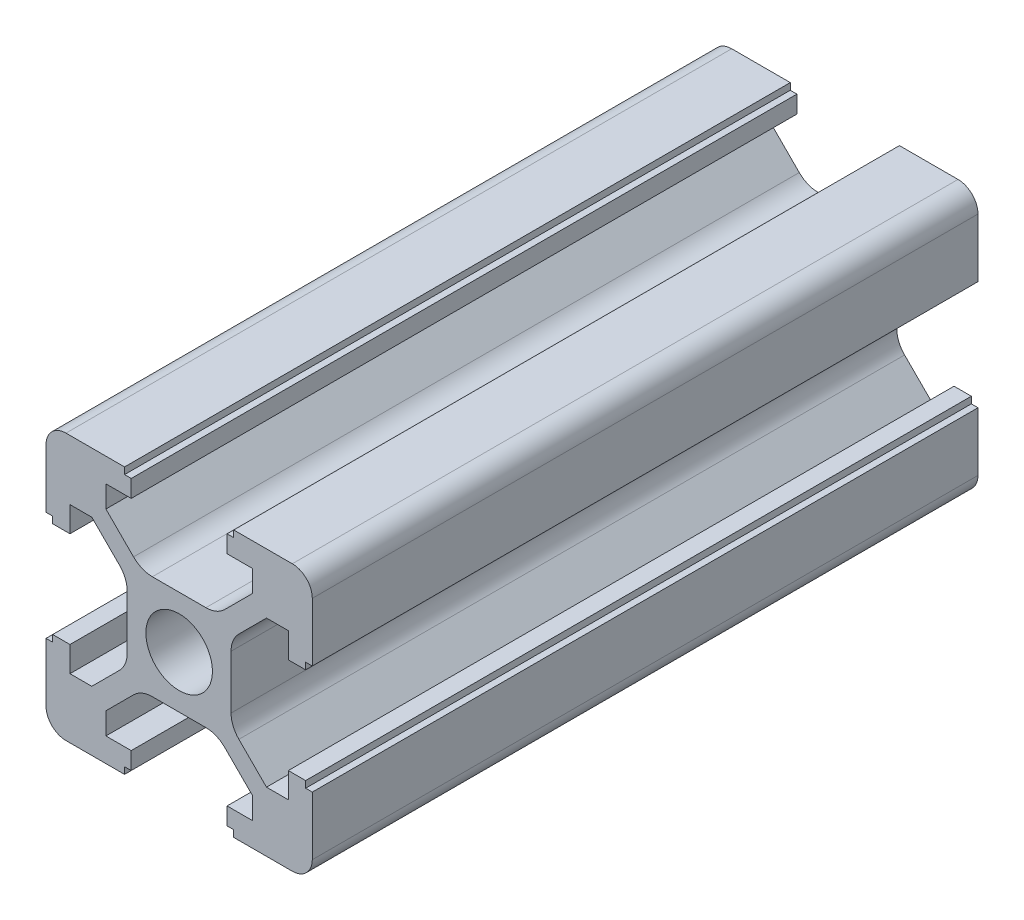
SolidWorks part; units mm, degrees
ref_plane "Front Plane" through (0, 0, 0) normal (0, 0, 1) x (1, 0, 0)
ref_plane "Top Plane" through (0, 0, 0) normal (0, 1, 0) x (1, 0, 0)
ref_plane "Right Plane" through (0, 0, 0) normal (1, 0, 0) x (0, 0, -1)
sketch "Sketch1" plane through (0, 0, 0) normal (0, 0, 1) x (1, 0, 0)
  line L0 (10, -4.1) -> (10, -8.5)
  line L1 (4.1, 10) -> (8.5, 10)
  line L2 (8.5, -10) -> (4.1, -10)
  line L3 (-8.5, -10) -> (-4.1, -10)
  line L4 (10, 8.5) -> (10, 4.1)
  line L7 (8.5, 10) -> (4.1, 10)
  line L8 (5.5, 6.5607) -> (3.4251, 4.4858)
  line L9 (8.5, 10) -> (4.1, 10)
  line L10 (3.9, 2.0109) -> (3.9, -2.0109)
  line L11 (2.0109, -3.9) -> (-2.0109, -3.9)
  line L12 (-3.9, -2.0109) -> (-3.9, 2.0109)
  line L13 (-2.0109, 3.9) -> (2.8393, 3.9)
  line L14 (2.5, 0) -> (22.2403, 0) construction
  line L15 (3.6, 9.5) -> (3.6, 8.2)
  line L16 (9.5, 3.6) -> (8.2, 3.6)
  line L17 (8.2, 3.6) -> (8.2, 5.5)
  line L18 (8.2, 5.5) -> (6.5607, 5.5)
  line L19 (10, -4.1) -> (10, -8.5)
  line L20 (4.1, 9.5) -> (3.6, 9.5)
  line L21 (4.1, 10) -> (4.1, 9.5)
  line L22 (8.5, 10) -> (4.1, 10)
  line L23 (10, 4.1) -> (9.5, 4.1)
  line L24 (9.5, 4.1) -> (9.5, 3.6)
  line L25 (5.5, 8.2) -> (5.5, 6.5607)
  line L26 (3.6, 8.2) -> (5.5, 8.2)
  line L27 (4.4858, 3.4251) -> (6.5607, 5.5)
  line L28 (10, -8.5) -> (10, -4.1)
  line L29 (6.5607, -5.5) -> (4.4858, -3.4251)
  line L30 (10, -8.5) -> (10, -4.1)
  line L31 (2.0109, -3.9) -> (-2.0109, -3.9)
  line L32 (3.9, 2.8393) -> (3.9, -2.0109)
  line L33 (9.5, -3.6) -> (8.2, -3.6)
  line L34 (3.6, -9.5) -> (3.6, -8.2)
  line L35 (3.6, -8.2) -> (5.5, -8.2)
  line L36 (5.5, -8.2) -> (5.5, -6.5607)
  line L37 (9.5, -4.1) -> (9.5, -3.6)
  line L38 (10, -4.1) -> (9.5, -4.1)
  line L39 (10, -8.5) -> (10, -4.1)
  line L40 (4.1, -10) -> (4.1, -9.5)
  line L41 (4.1, -9.5) -> (3.6, -9.5)
  line L42 (8.2, -5.5) -> (6.5607, -5.5)
  line L43 (8.2, -3.6) -> (8.2, -5.5)
  line L44 (3.4251, -4.4858) -> (5.5, -6.5607)
  line L45 (-4.1, -10) -> (-8.5, -10)
  line L46 (-10, -8.5) -> (-10, -4.1)
  line L47 (-8.5, -10) -> (-4.1, -10)
  line L48 (-5.5, -6.5607) -> (-3.4251, -4.4858)
  line L49 (-8.5, -10) -> (-4.1, -10)
  line L50 (-3.9, -2.0109) -> (-3.9, 2.0109)
  line L51 (2.0109, -3.9) -> (-2.0109, -3.9)
  line L52 (-3.6, -9.5) -> (-3.6, -8.2)
  line L53 (-9.5, -3.6) -> (-8.2, -3.6)
  line L54 (-8.2, -3.6) -> (-8.2, -5.5)
  line L55 (-8.2, -5.5) -> (-6.5607, -5.5)
  line L56 (-4.1, -9.5) -> (-3.6, -9.5)
  line L57 (-4.1, -10) -> (-4.1, -9.5)
  line L58 (-8.5, -10) -> (-4.1, -10)
  line L59 (-10, -4.1) -> (-9.5, -4.1)
  line L60 (-9.5, -4.1) -> (-9.5, -3.6)
  line L61 (-5.5, -8.2) -> (-5.5, -6.5607)
  line L62 (-3.6, -8.2) -> (-5.5, -8.2)
  line L63 (-4.4858, -3.4251) -> (-6.5607, -5.5)
  line L64 (-10, 4.1) -> (-10, 8.5)
  line L65 (-8.5, 10) -> (-4.1, 10)
  line L66 (-10, 8.5) -> (-10, 4.1)
  line L67 (-6.5607, 5.5) -> (-4.4858, 3.4251)
  line L68 (-10, 8.5) -> (-10, 4.1)
  line L69 (-2.0109, 3.9) -> (2.0109, 3.9)
  line L70 (-3.9, -2.0109) -> (-3.9, 2.0109)
  line L71 (-9.5, 3.6) -> (-8.2, 3.6)
  line L72 (-3.6, 9.5) -> (-3.6, 8.2)
  line L73 (-3.6, 8.2) -> (-5.5, 8.2)
  line L74 (-5.5, 8.2) -> (-5.5, 6.5607)
  line L75 (-9.5, 4.1) -> (-9.5, 3.6)
  line L76 (-10, 4.1) -> (-9.5, 4.1)
  line L77 (-10, 8.5) -> (-10, 4.1)
  line L78 (-4.1, 10) -> (-4.1, 9.5)
  line L79 (-4.1, 9.5) -> (-3.6, 9.5)
  line L80 (-8.2, 5.5) -> (-6.5607, 5.5)
  line L81 (-8.2, 3.6) -> (-8.2, 5.5)
  line L82 (-3.4251, 4.4858) -> (-5.5, 6.5607)
  line L83 (4.1, -10) -> (8.5, -10)
  arc A0 (2.0109, -3.9) -> (3.4251, -4.4858) centre (2.0109, -5.9) cw
  arc A1 (4.4858, -3.4251) -> (3.9, -2.0109) centre (5.9, -2.0109) cw
  arc A2 (3.9, 2.0109) -> (4.4858, 3.4251) centre (5.9, 2.0109) cw
  arc A3 (2.0109, 3.9) -> (3.4251, 4.4858) centre (2.0109, 5.9) ccw
  arc A4 (-2.0109, 3.9) -> (-3.4251, 4.4858) centre (-2.0109, 5.9) cw
  arc A5 (-4.4858, 3.4251) -> (-3.9, 2.0109) centre (-5.9, 2.0109) cw
  arc A6 (-3.4251, -4.4858) -> (-2.0109, -3.9) centre (-2.0109, -5.9) cw
  arc A7 (-3.9, -2.0109) -> (-4.4858, -3.4251) centre (-5.9, -2.0109) cw
  circle A8 centre (0, 0) radius 2.5
  arc A9 (-8.5, -10) -> (-10, -8.5) centre (-8.5, -8.5) cw
  arc A10 (-10, 8.5) -> (-8.5, 10) centre (-8.5, 8.5) cw
  arc A11 (8.5, 10) -> (10, 8.5) centre (8.5, 8.5) cw
  arc A12 (8.5, -10) -> (10, -8.5) centre (8.5, -8.5) ccw
  point P0 (0, 0)
  point P86 (0, 0)
  point P107 (10, -10)
  dimension "D3" = 2
  dimension "D5" = 5
  dimension "D2" = 1.5
  dimension "D8" = 1.5
  dimension "D4" = 6.1
  dimension "D6" = 4
  dimension "D11" = 0.5
  dimension "D12" = 0.5
extrude "Boss-Extrude2" add sketch "Sketch1" along normal blind 50
